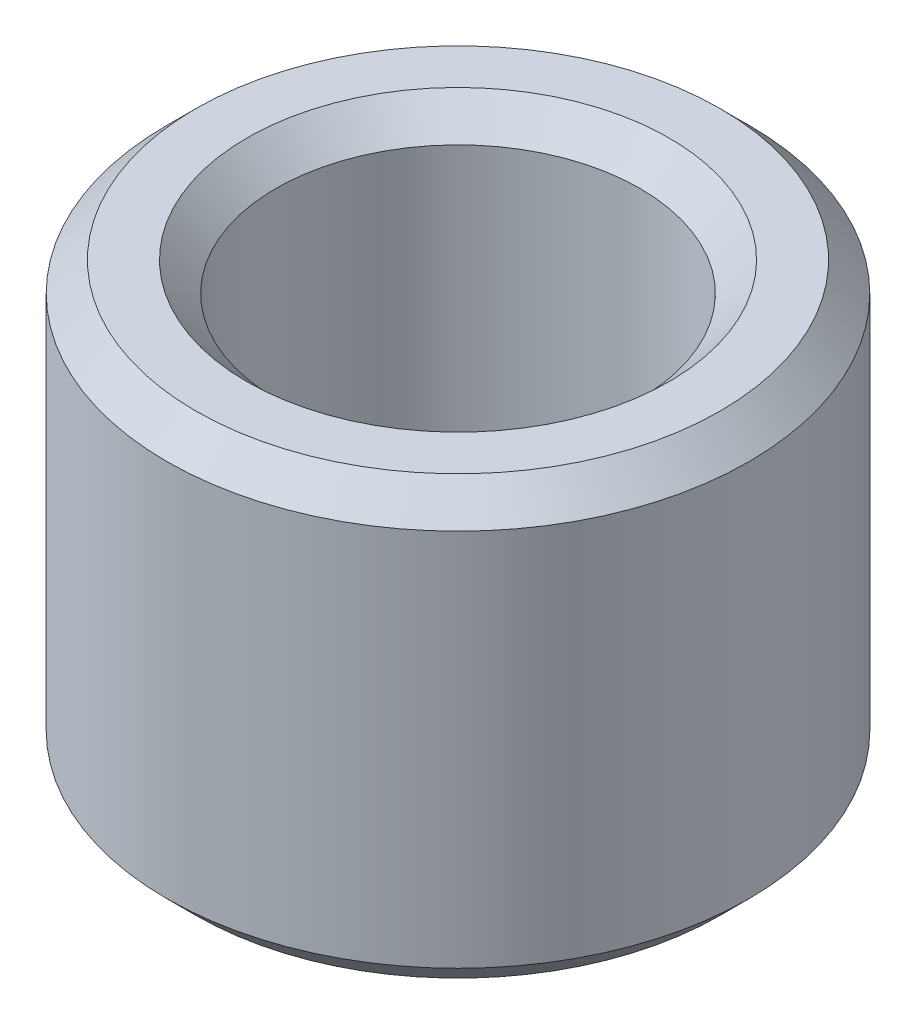
SolidWorks part; units mm, degrees
ref_plane "Front Plane" through (0, 0, 0) normal (0, 0, 1) x (1, 0, 0)
ref_plane "Top Plane" through (0, 0, 0) normal (0, 1, 0) x (1, 0, 0)
ref_plane "Right Plane" through (0, 0, 0) normal (1, 0, 0) x (0, 0, -1)
sketch "Sketch1" plane through (0, 0, 0) normal (0, 1, 0) x (1, 0, 0)
  circle A0 centre (0, 0) radius 1.25
  circle A1 centre (0, 0) radius 2
extrude "Boss-Extrude1" add sketch "Sketch1" along normal blind 3
chamfer "Chamfer1" distance 0.2 angle 45 4 edges at (0, 0, 1.25) (0, 3, 1.25) (0, 0, 2) (0, 3, 2)
